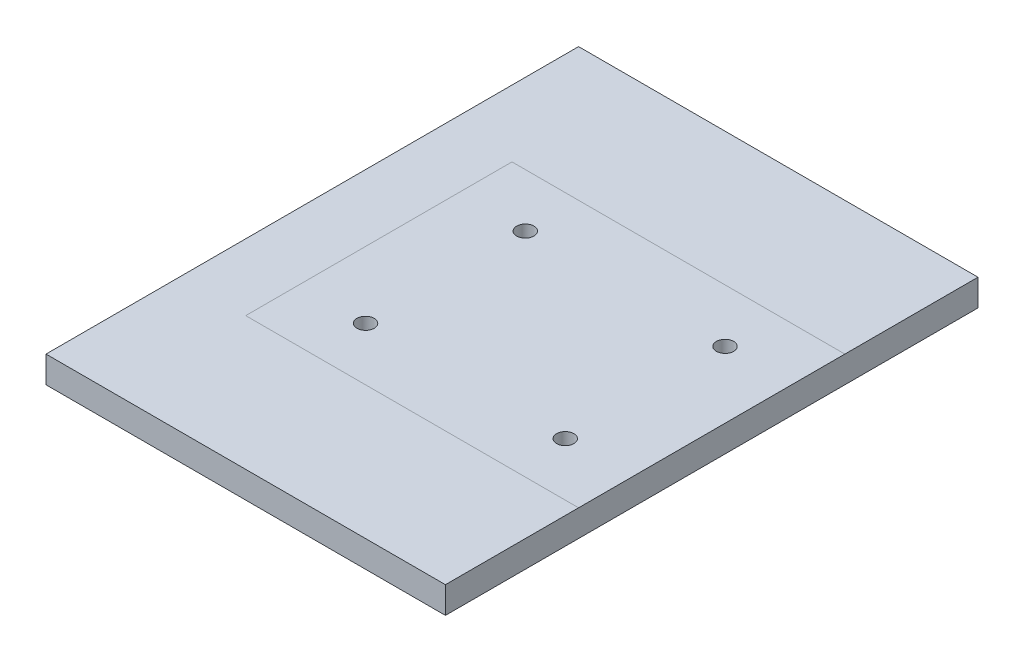
SolidWorks part; units mm, degrees
ref_plane "Front Plane" through (0, 0, 0) normal (0, 0, 1) x (1, 0, 0)
ref_plane "Top Plane" through (0, 0, 0) normal (0, 1, 0) x (1, 0, 0)
ref_plane "Right Plane" through (0, 0, 0) normal (1, 0, 0) x (0, 0, -1)
sketch "Sketch1" plane through (0, 0, 0) normal (0, 1, 0) x (1, 0, 0)
  line L1 (-150, 200) -> (150, 200)
  line L2 (-150, 200) -> (-150, -200)
  line L3 (-150, -200) -> (150, -200)
  line L4 (150, 200) -> (150, -200)
  dimension "D1" = 300
  dimension "D2" = 400
  dimension "D3" = 200
  dimension "D4" = 150
extrude "Support Plate" add sketch "Sketch1" against normal blind 20
sketch "Sketch2" plane through (0, 0, 0) normal (0, 1, 0) x (-1, 0, 0)
  line L0 (-150, 200) -> (-150, -200) construction
  circle A0 centre (-100, -60) radius 6.5
  circle A1 centre (50, -60) radius 6.5
  circle A2 centre (50, 60) radius 6.5
  circle A3 centre (-100, 60) radius 6.5
  dimension "D9" = 13
  dimension "D10" = 13
  dimension "D11" = 13
  dimension "D12" = 13
  dimension "D1" = 50
  dimension "D2" = 200
  dimension "D3" = 50
  dimension "D4" = 200
  dimension "D5" = 60
  dimension "D6" = 60
  dimension "D7" = 60
  dimension "D8" = 60
extrude "Bolt Holes" cut sketch "Sketch2" against normal through all
ref_plane "Plane1" through (0, 50, 0) normal (0, 1, 0) x (-1, 0, 0)
sketch "Sketch3" plane through (0, 50, 0) normal (0, 1, 0) x (-1, 0, 0)
  line L0 (-150, 200) -> (-150, -200) construction
  line L1 (-150, -100) -> (100, -100)
  line L2 (-150, -100) -> (-150, 100)
  line L3 (-150, 100) -> (100, 100)
  line L4 (100, -100) -> (100, 100)
  dimension "D1" = 200
  dimension "D2" = 250
  dimension "D3" = 100
split line "Split Line1 Outlines Contact area"
